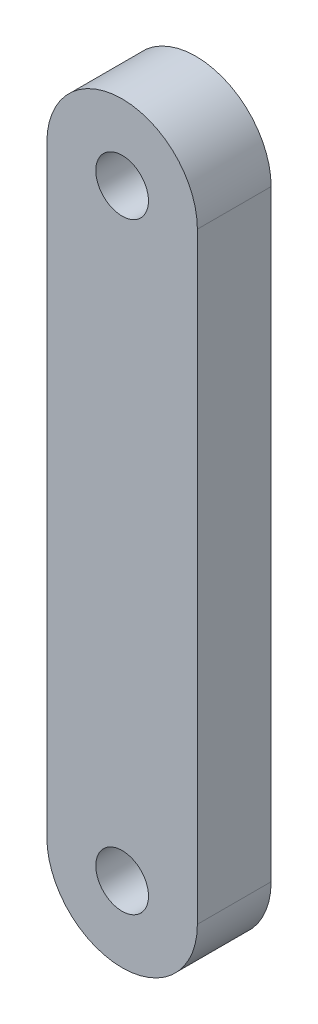
SolidWorks part; units mm, degrees
ref_plane "Front Plane" through (0, 0, 0) normal (0, 0, 1) x (1, 0, 0)
ref_plane "Top Plane" through (0, 0, 0) normal (0, 1, 0) x (1, 0, 0)
ref_plane "Right Plane" through (0, 0, 0) normal (1, 0, 0) x (0, 0, -1)
sketch "Sketch3" plane through (0, 0, 0) normal (0, 0, 1) x (1, 0, 0)
  line L0 (-4.9786, 17.9209) -> (-4.9786, -22.0791)
  line L1 (5.0214, 17.9209) -> (5.0214, -22.0791)
  arc A0 (-4.9786, 17.9209) -> (5.0214, 17.9209) centre (0.0214, 17.9209) cw
  arc A1 (-4.9786, -22.0791) -> (5.0214, -22.0791) centre (0.0214, -22.0791) ccw
  circle A2 centre (0.0214, 17.9209) radius 1.75
  circle A3 centre (0.0214, -22.0791) radius 1.75
  point P10 (0, 0)
  point P11 (0, 0)
  point P12 (0, 0)
  point P13 (0, 0)
  point P14 (0, 0)
  point P15 (0, 0)
  point P16 (0, 0)
  point P17 (0, 0)
  dimension "D1" = 10
  dimension "D2" = 40
  dimension "D3" = 3.5
extrude "Boss-Extrude1" add sketch "Sketch3" along normal blind 4.9
equation "\"width_body\"= 10mm"
equation "\"height_body\"= 24mm"
